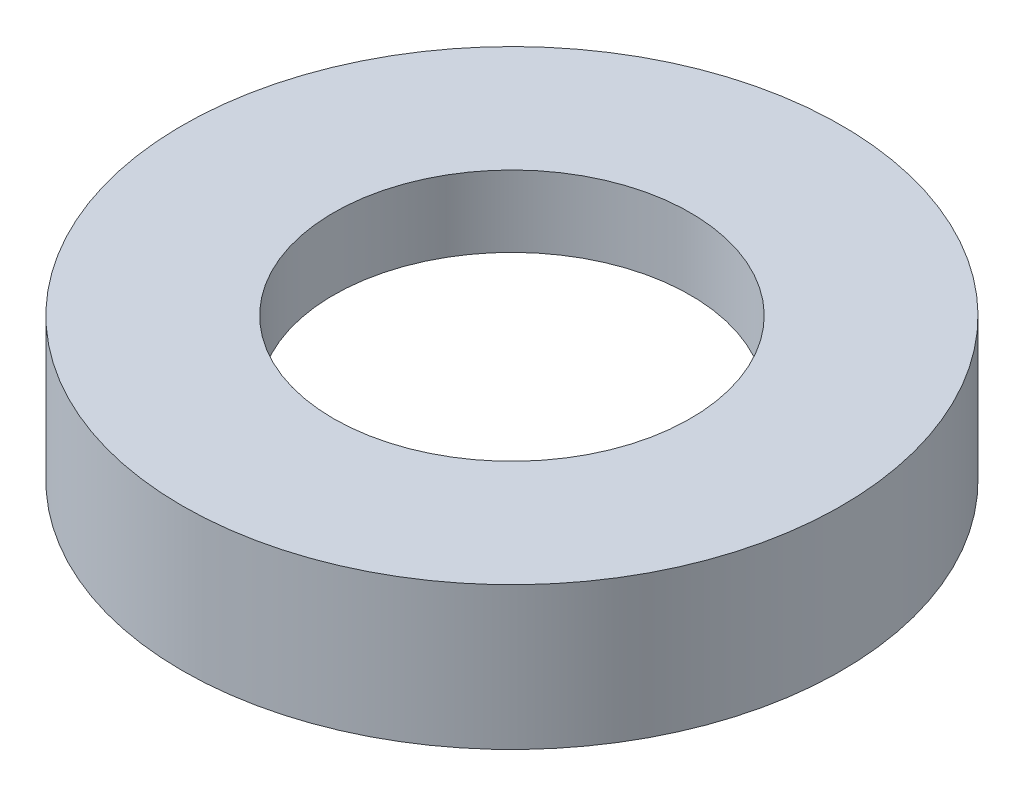
SolidWorks part; units mm, degrees
ref_plane "前视基准面" through (0, 0, 0) normal (0, 0, 1) x (1, 0, 0)
ref_plane "上视基准面" through (0, 0, 0) normal (0, 1, 0) x (1, 0, 0)
ref_plane "右视基准面" through (0, 0, 0) normal (1, 0, 0) x (0, 0, -1)
sketch "草图1" plane through (0, 0, 0) normal (0, 0, 1) x (1, 0, 0)
  line L0 (0, 60.0208) -> (0, -56.4315) construction
  line L1 (23.5, 0) -> (23.5, 4.5)
  line L2 (23.5, 4.5) -> (24.1, 4.5)
  line L3 (24.1, 4.5) -> (24.1, 5.5)
  line L4 (24.1, 5.5) -> (13.75, 5.5)
  line L5 (13.75, 5.5) -> (13.75, 11)
  line L6 (13.75, 11) -> (25.4, 11)
  line L7 (25.4, 11) -> (25.4, 0)
  line L8 (25.4, 0) -> (23.5, 0)
  point P5 (18.925, 5.5)
  dimension "D1" = 25.4
  dimension "D2" = 13.75
  dimension "D3" = 24.1
  dimension "D4" = 23.5
  dimension "D5" = 1
  dimension "D6" = 5.5
  dimension "D7" = 11
revolve "旋转1" add sketch "草图1" angle 360 about L0
cosmetic thread "装饰螺纹线1" parameters "D2"=28.5
cosmetic thread "装饰螺纹线2" parameters "D2"=48
